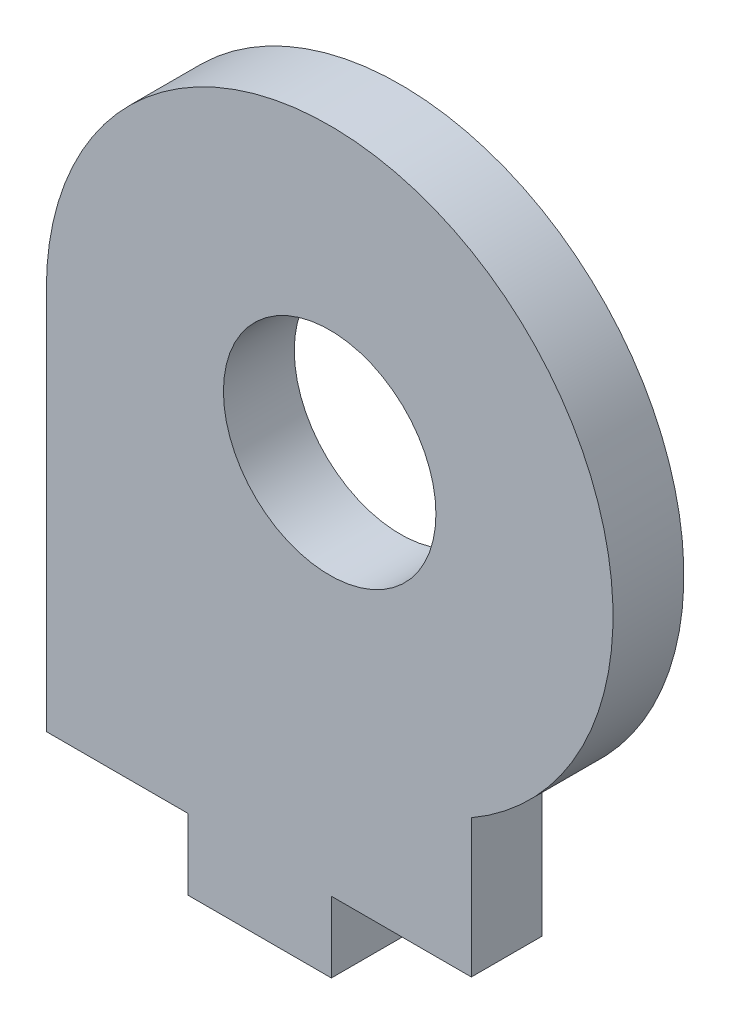
SolidWorks part; units mm, degrees
ref_plane "Front Plane" through (0, 0, 0) normal (0, 0, 1) x (1, 0, 0)
ref_plane "Top Plane" through (0, 0, 0) normal (0, 1, 0) x (1, 0, 0)
ref_plane "Right Plane" through (0, 0, 0) normal (1, 0, 0) x (0, 0, -1)
sketch "Sketch1" plane through (0, 0, 0) normal (0, 0, 1) x (1, 0, 0)
  line L0 (7.9877, 0) -> (20.6877, 0) construction
  line L1 (20.6877, 0) -> (20.6877, 20.3568) construction
  line L2 (20.6877, 20.3568) -> (20.6877, 33.0568) construction
  line L3 (20.6877, 20.3568) -> (15.9252, 20.3568) construction
  line L5 (7.9877, 20.3568) -> (7.9877, 0)
  line L12 (33.2915, 21.9172) -> (33.2915, 0) construction
  line L13 (7.9877, 0) -> (27.0377, 0)
  line L14 (27.0377, 0) -> (27.0377, 9.3583)
  circle A0 centre (20.6877, 20.3568) radius 4.7625
  arc A10 (27.0377, 9.3583) -> (7.9877, 20.3568) centre (20.6877, 20.3568) ccw
  arc A11 (27.0377, 9.3583) -> (20.6877, 7.6568) centre (20.6877, 20.3568) ccw construction
  dimension "D2" = 9.525
  dimension "D4" = 19.05
  dimension "D1" = 20.3568
extrude "Boss-Extrude1" add sketch "Sketch1" along normal blind 3.175
sketch "Sketch2" plane through (0, 0, 0) normal (0, -1, 0) x (1, 0, 0)
  line L0 (7.9877, 3.175) -> (27.0377, 3.175) construction
  line L1 (7.9877, 0) -> (14.3377, 0)
  line L2 (7.9877, 0) -> (7.9877, 3.175)
  line L3 (7.9877, 3.175) -> (14.3377, 3.175)
  line L4 (14.3377, 0) -> (14.3377, 3.175)
  line L6 (27.0377, 0) -> (20.7639, 0)
  line L7 (27.0377, 0) -> (27.0377, 3.175)
  line L8 (27.0377, 3.175) -> (20.7639, 3.175)
  line L9 (20.7639, 0) -> (20.7639, 3.175)
  dimension "D1" = 6.35
  dimension "D2" = 6.4262
extrude "Cut-Extrude1" cut sketch "Sketch2" against normal blind 3.175
